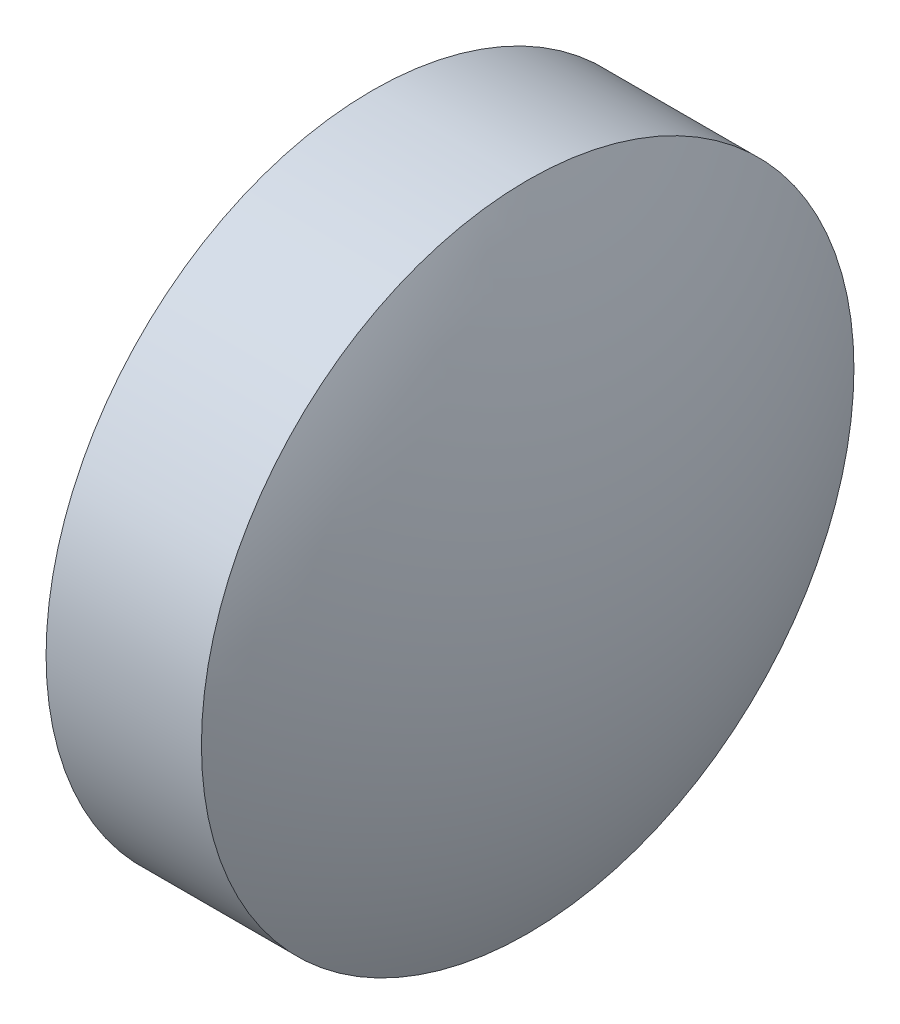
SolidWorks part; units mm, degrees
ref_plane "前视基准面" through (0, 0, 0) normal (0, 0, 1) x (1, 0, 0)
ref_plane "上视基准面" through (0, 0, 0) normal (0, 1, 0) x (1, 0, 0)
ref_plane "右视基准面" through (0, 0, 0) normal (1, 0, 0) x (0, 0, -1)
sketch "草图1" plane through (0, 0, 0) normal (0, 0, 1) x (1, 0, 0)
  line L0 (400.3278, 12.4457) -> (405.7228, 12.4457) construction
  line L1 (401.1885, 12.4457) -> (401.1885, 15.5957)
  line L2 (401.1885, 15.5957) -> (402.6885, 15.5957)
  line L3 (403.4485, 12.4457) -> (401.1885, 12.4457)
  arc A0 (403.4485, 12.4457) -> (402.6885, 15.5957) centre (396.5405, 12.4457) ccw
revolve "旋转1" add sketch "草图1" angle 360 about L0
